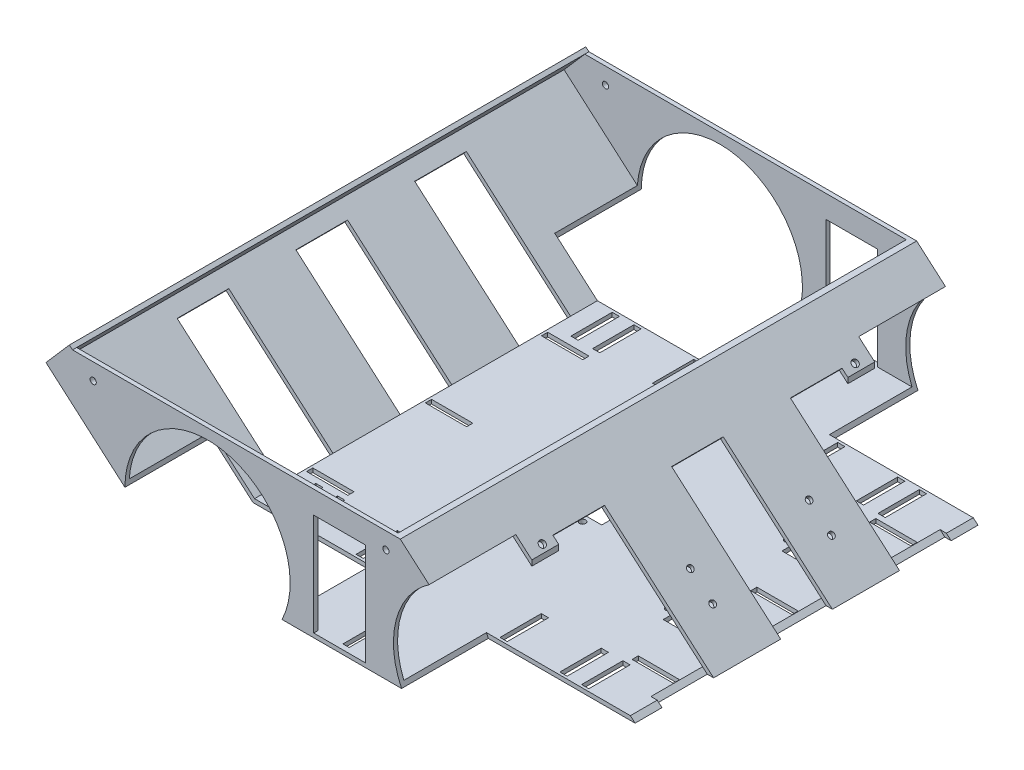
SolidWorks part; units mm, degrees
material "AISI 304"
ref_plane "前视基准面" through (0, 0, 0) normal (0, 0, 1) x (1, 0, 0)
ref_plane "上视基准面" through (0, 0, 0) normal (0, 1, 0) x (1, 0, 0)
ref_plane "右视基准面" through (0, 0, 0) normal (1, 0, 0) x (0, 0, -1)
sketch "草图1" plane through (0, 0, 0) normal (0, 0, 1) x (1, 0, 0)
  line L0 (0, 0) -> (-185, 0)
  line L1 (-185, 0) -> (-256.6974, 62.3256)
  line L2 (-256.6974, 62.3256) -> (-71.6974, 62.3256)
  line L3 (-71.6974, 62.3256) -> (0, 0)
extrude "凸台-拉伸1" add sketch "草图1" along normal blind 250
shell "抽壳1" thickness 2
sketch "草图4" plane through (0, 0, 250) normal (0, 0, 1) x (1, 0, 0)
  circle A0 centre (-35, 17.3) radius 40
  circle A1 centre (-165, 17.3) radius 40
extrude "切除-拉伸3" cut sketch "草图4" against normal blind 42
sketch "草图6" plane through (0, 0, 0) normal (0, 0, -1) x (-1, 0, 0)
  arc A0 (15.1851, -17.4472) -> (15.1851, 52.0472) centre (35, 17.3) ccw
  arc A1 (15.1851, 52.0472) -> (15.1851, -17.4472) centre (-5, 17.3) ccw
  circle A2 centre (165, 17.3) radius 40
extrude "切除-拉伸5" cut sketch "草图6" against normal blind 42 contours A2 | A0 A1
sketch "草图7" plane through (0, 2, 0) normal (0, 1, 0) x (1, 0, 0)
  line L0 (-184.2522, -125) -> (127.4873, -125) construction
  line L1 (-184.2522, -208) -> (-184.2522, -42) construction
  line L2 (-175.84, -206.75) -> (-172.34, -206.75)
  line L7 (-175.84, -206.75) -> (-175.84, -186.75)
  line L8 (-175.84, -186.75) -> (-172.34, -186.75)
  line L9 (-172.34, -206.75) -> (-172.34, -186.75)
  line L10 (-27.16, -206.75) -> (-23.66, -206.75)
  line L11 (-27.16, -206.75) -> (-27.16, -186.75)
  line L12 (-27.16, -186.75) -> (-23.66, -186.75)
  line L13 (-23.66, -206.75) -> (-23.66, -186.75)
  line L14 (-165.34, -206.75) -> (-161.84, -206.75)
  line L15 (-165.34, -206.75) -> (-165.34, -186.75)
  line L16 (-165.34, -186.75) -> (-161.84, -186.75)
  line L17 (-161.84, -206.75) -> (-161.84, -186.75)
  line L18 (-136.34, -206.75) -> (-132.84, -206.75)
  line L19 (-136.34, -206.75) -> (-136.34, -186.75)
  line L20 (-136.34, -186.75) -> (-132.84, -186.75)
  line L21 (-132.84, -206.75) -> (-132.84, -186.75)
  line L22 (-34.16, -206.75) -> (-37.66, -206.75)
  line L23 (-34.16, -206.75) -> (-34.16, -186.75)
  line L24 (-34.16, -186.75) -> (-37.66, -186.75)
  line L25 (-37.66, -206.75) -> (-37.66, -186.75)
  line L26 (-63.16, -206.75) -> (-66.66, -206.75)
  line L27 (-63.16, -206.75) -> (-63.16, -186.75)
  line L28 (-63.16, -186.75) -> (-66.66, -186.75)
  line L29 (-66.66, -206.75) -> (-66.66, -186.75)
  line L30 (-132.84, -43.25) -> (-132.84, -63.25)
  line L31 (-136.34, -63.25) -> (-132.84, -63.25)
  line L32 (-136.34, -43.25) -> (-136.34, -63.25)
  line L33 (-136.34, -43.25) -> (-132.84, -43.25)
  line L34 (-161.84, -43.25) -> (-161.84, -63.25)
  line L35 (-165.34, -63.25) -> (-161.84, -63.25)
  line L36 (-165.34, -43.25) -> (-165.34, -63.25)
  line L37 (-165.34, -43.25) -> (-161.84, -43.25)
  line L38 (-172.34, -43.25) -> (-172.34, -63.25)
  line L39 (-175.84, -63.25) -> (-172.34, -63.25)
  line L40 (-175.84, -43.25) -> (-175.84, -63.25)
  line L41 (-175.84, -43.25) -> (-172.34, -43.25)
  line L42 (-66.66, -43.25) -> (-66.66, -63.25)
  line L43 (-63.16, -63.25) -> (-66.66, -63.25)
  line L44 (-63.16, -43.25) -> (-63.16, -63.25)
  line L45 (-63.16, -43.25) -> (-66.66, -43.25)
  line L46 (-37.66, -43.25) -> (-37.66, -63.25)
  line L47 (-34.16, -63.25) -> (-37.66, -63.25)
  line L48 (-34.16, -43.25) -> (-34.16, -63.25)
  line L49 (-34.16, -43.25) -> (-37.66, -43.25)
  line L50 (-23.66, -43.25) -> (-23.66, -63.25)
  line L51 (-27.16, -63.25) -> (-23.66, -63.25)
  line L52 (-27.16, -43.25) -> (-27.16, -63.25)
  line L53 (-27.16, -43.25) -> (-23.66, -43.25)
  line L54 (-24.66, -90.25) -> (-24.66, -105.5276) construction
  line L55 (-101.1743, -135) -> (-89.1743, -135)
  line L56 (-101.1743, -135) -> (-101.1743, -115)
  line L57 (-101.1743, -115) -> (-89.1743, -115)
  line L58 (-89.1743, -135) -> (-89.1743, -115)
  line L59 (-101.1743, -135) -> (-89.1743, -115) construction
  line L60 (-101.1743, -115) -> (-89.1743, -135) construction
  line L61 (-34.66, -90.25) -> (-14.66, -90.25)
  line L62 (-34.66, -90.25) -> (-34.66, -102.25)
  line L63 (-34.66, -102.25) -> (-14.66, -102.25)
  line L64 (-14.66, -90.25) -> (-14.66, -102.25)
  line L65 (-14.66, -159.75) -> (-14.66, -147.75)
  line L66 (-34.66, -147.75) -> (-14.66, -147.75)
  line L67 (-34.66, -159.75) -> (-34.66, -147.75)
  line L68 (-34.66, -159.75) -> (-14.66, -159.75)
  circle A0 centre (-95.1743, -111.75) radius 1.5
  circle A1 centre (-95.1743, -138.25) radius 1.5
  circle A2 centre (-11.41, -96.25) radius 1.5
  circle A3 centre (-37.91, -96.25) radius 1.5
  circle A4 centre (-37.91, -153.75) radius 1.5
  circle A5 centre (-11.41, -153.75) radius 1.5
  point P52 (-95.1743, -125)
  dimension "D2" = 29
  dimension "D3" = 26.5
  dimension "D6" = 3
  dimension "D1" = 10.5
  dimension "D4" = 26.5
  dimension "D5" = 20
  dimension "D7" = 81.75
  dimension "D8" = 81.75
  dimension "D9" = 81.75
  dimension "D10" = 81.75
extrude "切除-拉伸6" cut sketch "草图7" against normal blind 32
sketch "草图8" plane through (0, 0, 208) normal (0, 0, 1) x (1, 0, 0)
  line L1 (-50, 52) -> (0, 52)
  line L2 (-50, 52) -> (-50, 2)
  line L3 (-50, 2) -> (0, 2)
  line L4 (0, 52) -> (0, 2)
extrude "切除-拉伸7" cut sketch "草图8" against normal blind 15
sketch "草图9" plane through (0, 0, 42) normal (0, 0, -1) x (-1, 0, 0)
  line L0 (50, 2) -> (0, 2)
  line L2 (0, 2) -> (0, 50)
  line L3 (0, 50) -> (50, 50)
  line L4 (50, 2) -> (50, 50)
  line L5 (5.3492, 2) -> (71.9582, 2) construction
extrude "切除-拉伸8" cut sketch "草图9" against normal blind 15
sketch "草图10" plane through (0, 0, 0) normal (0.6561, 0.7547, 0) x (0.7547, -0.6561, 0)
  line L0 (0, -208) -> (0, -42) construction
  line L1 (0, -170) -> (-70, -170)
  line L2 (0, -170) -> (0, -195)
  line L3 (0, -195) -> (-70, -195)
  line L4 (-70, -170) -> (-70, -195)
  line L6 (0, -55) -> (-70, -55)
  line L7 (0, -55) -> (0, -80)
  line L8 (0, -80) -> (-70, -80)
  line L9 (-70, -55) -> (-70, -80)
  line L10 (0, -112.5) -> (-70, -112.5)
  line L11 (0, -112.5) -> (0, -137.5)
  line L12 (0, -137.5) -> (-70, -137.5)
  line L13 (-70, -112.5) -> (-70, -137.5)
extrude "切除-拉伸9" cut sketch "草图10" against normal blind 2
sketch "草图13" plane through (0, 0, 0) normal (0, 0, -1) x (-1, 0, 0)
  line L1 (88.6038, 51.4288) -> (113.6038, 51.4288)
  line L2 (88.6038, 51.4288) -> (88.6038, 2)
  line L4 (113.6038, 51.4288) -> (113.6038, 2)
  line L5 (88.6038, 2) -> (113.6038, 2)
extrude "切除-拉伸10" cut sketch "草图13" against normal blind 304
sketch "草图14" plane through (-78.3144, -90.0904, 0) normal (0.6561, 0.7547, 0) x (0.7547, -0.6561, 0)
  line L0 (-140.369, -208) -> (-140.369, -42) construction
  line L1 (-140.369, -55) -> (-207.2252, -55)
  line L2 (-140.369, -55) -> (-140.369, -80)
  line L3 (-140.369, -80) -> (-207.2252, -80)
  line L4 (-207.2252, -55) -> (-207.2252, -80)
  line L6 (-140.369, -112.5) -> (-207.2252, -112.5)
  line L7 (-140.369, -112.5) -> (-140.369, -137.5)
  line L8 (-140.369, -137.5) -> (-207.2252, -137.5)
  line L9 (-207.2252, -112.5) -> (-207.2252, -137.5)
  line L10 (-140.369, -170) -> (-207.2252, -170)
  line L11 (-140.369, -170) -> (-140.369, -195)
  line L12 (-140.369, -195) -> (-207.2252, -195)
  line L13 (-207.2252, -170) -> (-207.2252, -195)
extrude "切除-拉伸11" cut sketch "草图14" against normal blind 2
sketch "草图15" plane through (0, 0, 0) normal (0, -1, 0) x (1, 0, 0)
  line L5 (-185.5643, 195) -> (-160.5643, 195) construction
  line L6 (-185.5643, 195) -> (-185.5643, 170) construction
  line L7 (-185.5643, 170) -> (-160.5643, 170) construction
  line L8 (-160.5643, 195) -> (-160.5643, 170) construction
  line L13 (-128.9346, 250) -> (-71.0654, 250) construction
  line L14 (-185.5643, 80) -> (-160.5643, 80) construction
  line L15 (-185.5643, 80) -> (-185.5643, 57.495) construction
  line L16 (-185.5643, 57.495) -> (-160.5643, 57.495) construction
  line L17 (-160.5643, 80) -> (-160.5643, 57.495) construction
  line L18 (-3.0485, 195) -> (-27.8654, 195) construction
  line L19 (-3.0485, 195) -> (-3.0485, 170) construction
  line L20 (-3.0485, 170) -> (-27.8654, 170) construction
  line L21 (-27.8654, 195) -> (-27.8654, 170) construction
  line L22 (-3.0485, 137.5) -> (-28.0485, 137.5) construction
  line L23 (-3.0485, 137.5) -> (-3.0485, 112.5) construction
  line L24 (-3.0485, 112.5) -> (-28.0485, 112.5) construction
  line L25 (-28.0485, 137.5) -> (-28.0485, 112.5) construction
  line L26 (-3.0485, 80) -> (-28.0485, 80) construction
  line L27 (-3.0485, 80) -> (-3.0485, 54.8155) construction
  line L28 (-3.0485, 54.8155) -> (-28.0485, 54.8155) construction
  line L29 (-28.0485, 80) -> (-28.0485, 54.8155) construction
  line L30 (-185.5643, 137.5) -> (-160.5643, 137.5) construction
  line L31 (-185.5643, 137.5) -> (-185.5643, 112.5) construction
  line L32 (-185.5643, 112.5) -> (-160.5643, 112.5) construction
  line L33 (-160.5643, 137.5) -> (-160.5643, 112.5) construction
  line L34 (-113.9749, 250) -> (-86.951, 250) construction
  line L35 (-113.9749, 250) -> (-113.9749, 225) construction
  line L36 (-113.9749, 225) -> (-86.951, 225) construction
  line L37 (-86.951, 250) -> (-86.951, 225) construction
  line L38 (-128.9346, 0) -> (-71.0654, 0) construction
  line L39 (-113.2875, 0) -> (-88.2875, 0) construction
  line L40 (-113.2875, 0) -> (-113.2875, 25) construction
  line L41 (-113.2875, 25) -> (-88.2875, 25) construction
  line L42 (-88.2875, 0) -> (-88.2875, 25) construction
  line L43 (-86.951, 237.5) -> (-113.9749, 237.5) construction
  line L44 (-15.4569, 195) -> (-15.4569, 170) construction
  line L45 (-15.5485, 137.5) -> (-15.5485, 112.5) construction
  line L46 (-15.5485, 80) -> (-15.5485, 54.8155) construction
  line L47 (-88.2875, 12.5) -> (-113.2875, 12.5) construction
  line L48 (-173.0643, 195) -> (-173.0643, 170) construction
  line L49 (-173.0643, 137.5) -> (-173.0643, 112.5) construction
  line L50 (-173.0643, 80) -> (-173.0643, 57.495) construction
  line L52 (-98.963, 247.5) -> (-101.963, 247.5)
  line L53 (-98.963, 247.5) -> (-98.963, 227.5)
  line L54 (-98.963, 227.5) -> (-101.963, 227.5)
  line L55 (-101.963, 247.5) -> (-101.963, 227.5)
  line L56 (-98.963, 247.5) -> (-101.963, 227.5) construction
  line L57 (-98.963, 227.5) -> (-101.963, 247.5) construction
  line L58 (-5.4569, 184) -> (-25.4569, 184)
  line L59 (-5.4569, 184) -> (-5.4569, 181)
  line L60 (-5.4569, 181) -> (-25.4569, 181)
  line L61 (-25.4569, 184) -> (-25.4569, 181)
  line L62 (-5.4569, 184) -> (-25.4569, 181) construction
  line L63 (-5.4569, 181) -> (-25.4569, 184) construction
  line L64 (-5.5485, 126.5) -> (-25.5485, 126.5)
  line L65 (-5.5485, 126.5) -> (-5.5485, 123.5)
  line L66 (-5.5485, 123.5) -> (-25.5485, 123.5)
  line L67 (-25.5485, 126.5) -> (-25.5485, 123.5)
  line L68 (-5.5485, 126.5) -> (-25.5485, 123.5) construction
  line L69 (-5.5485, 123.5) -> (-25.5485, 126.5) construction
  line L70 (-5.5485, 68.9078) -> (-25.5485, 68.9078)
  line L71 (-5.5485, 68.9078) -> (-5.5485, 65.9078)
  line L72 (-5.5485, 65.9078) -> (-25.5485, 65.9078)
  line L73 (-25.5485, 68.9078) -> (-25.5485, 65.9078)
  line L74 (-5.5485, 68.9078) -> (-25.5485, 65.9078) construction
  line L75 (-5.5485, 65.9078) -> (-25.5485, 68.9078) construction
  line L76 (-99.2875, 22.5) -> (-102.2875, 22.5)
  line L77 (-99.2875, 22.5) -> (-99.2875, 2.5)
  line L78 (-99.2875, 2.5) -> (-102.2875, 2.5)
  line L79 (-102.2875, 22.5) -> (-102.2875, 2.5)
  line L80 (-99.2875, 22.5) -> (-102.2875, 2.5) construction
  line L81 (-99.2875, 2.5) -> (-102.2875, 22.5) construction
  line L82 (-163.0643, 70.2475) -> (-183.0643, 70.2475)
  line L83 (-163.0643, 70.2475) -> (-163.0643, 67.2475)
  line L84 (-163.0643, 67.2475) -> (-183.0643, 67.2475)
  line L85 (-183.0643, 70.2475) -> (-183.0643, 67.2475)
  line L86 (-163.0643, 70.2475) -> (-183.0643, 67.2475) construction
  line L87 (-163.0643, 67.2475) -> (-183.0643, 70.2475) construction
  line L88 (-163.0643, 126.5) -> (-183.0643, 126.5)
  line L89 (-163.0643, 126.5) -> (-163.0643, 123.5)
  line L90 (-163.0643, 123.5) -> (-183.0643, 123.5)
  line L91 (-183.0643, 126.5) -> (-183.0643, 123.5)
  line L92 (-163.0643, 126.5) -> (-183.0643, 123.5) construction
  line L93 (-163.0643, 123.5) -> (-183.0643, 126.5) construction
  line L94 (-163.0643, 184) -> (-183.0643, 184)
  line L95 (-163.0643, 184) -> (-163.0643, 181)
  line L96 (-163.0643, 181) -> (-183.0643, 181)
  line L97 (-183.0643, 184) -> (-183.0643, 181)
  line L98 (-163.0643, 184) -> (-183.0643, 181) construction
  line L99 (-163.0643, 181) -> (-183.0643, 184) construction
  point P58 (-100.463, 237.5)
  point P65 (-15.4569, 182.5)
  point P70 (-15.5485, 125)
  point P75 (-15.5485, 67.4078)
  point P80 (-100.7875, 12.5)
  point P85 (-173.0643, 68.7475)
  point P90 (-173.0643, 125)
  point P95 (-173.0643, 182.5)
extrude "切除-拉伸12" cut sketch "草图15" against normal blind 2
sketch "草图16" plane through (-1.3121, -1.5094, 0) normal (-0.6561, -0.7547, 0) x (0.7547, -0.6561, 0)
  circle A0 centre (-22.1612, 96.25) radius 1.5
  circle A1 centre (-36.4612, 96.25) radius 1.5
  circle A2 centre (-22.1612, 153.75) radius 1.5
  circle A3 centre (-36.4612, 153.75) radius 1.5
extrude "切除-拉伸13" cut sketch "草图16" against normal blind 90
sketch "草图18" plane through (0, 0, 0) normal (0.6561, 0.7547, 0) x (0.7547, -0.6561, 0)
  circle A0 centre (-69.1772, -200.7358) radius 1.6
  circle A1 centre (-69.1772, -49.2642) radius 1.6
extrude "切除-拉伸14" cut sketch "草图18" against normal blind 5
sketch "草图19" plane through (0, 0, 250) normal (0, 0, 1) x (1, 0, 0)
  line L0 (-256.6974, 62.3256) -> (-241.6974, 62.3256)
  line L1 (-71.6974, 62.3256) -> (-256.6974, 62.3256) construction
  line L3 (-256.6974, 62.3256) -> (-204.9999, 17.3857) construction
  line L5 (-256.6974, 62.3256) -> (-241.6974, 49.2863)
  line L6 (-241.6974, 49.2863) -> (-230.3625, 62.3256)
  line L7 (-230.3625, 62.3256) -> (-241.6974, 62.3256)
extrude "切除-拉伸15" cut sketch "草图19" against normal blind 264
sketch "草图20" plane through (-162.0709, 140.8861, 0) normal (-0.7547, 0.6561, 0) x (0, 0, 1)
  line L0 (0, -104.0937) -> (0, -121.3709) construction
  line L1 (0, -104.0937) -> (250, -104.0937)
  line L2 (0, -104.0937) -> (0, -121.3709)
  line L3 (0, -121.3709) -> (250, -121.3709)
  line L4 (250, -104.0937) -> (250, -121.3709)
extrude "凸台-拉伸2" add sketch "草图20" along normal blind 2
sketch "草图21" plane through (0, 0, 250) normal (0, 0, 1) x (1, 0, 0)
  line L0 (-88.6038, 51.4288) -> (-88.6038, 2) construction
  line L1 (-71.6974, 62.3256) -> (-230.3625, 62.3256) construction
  circle A0 centre (-78.6038, 54.3256) radius 1.5
  circle A1 centre (-220.3625, 54.3256) radius 1.5
  dimension "D1" = 3
  dimension "D4" = 3
  dimension "D2" = 10
  dimension "D3" = 8
  dimension "D5" = 10
extrude "切除-拉伸17" cut sketch "草图21" against normal through all both and the other way through all
